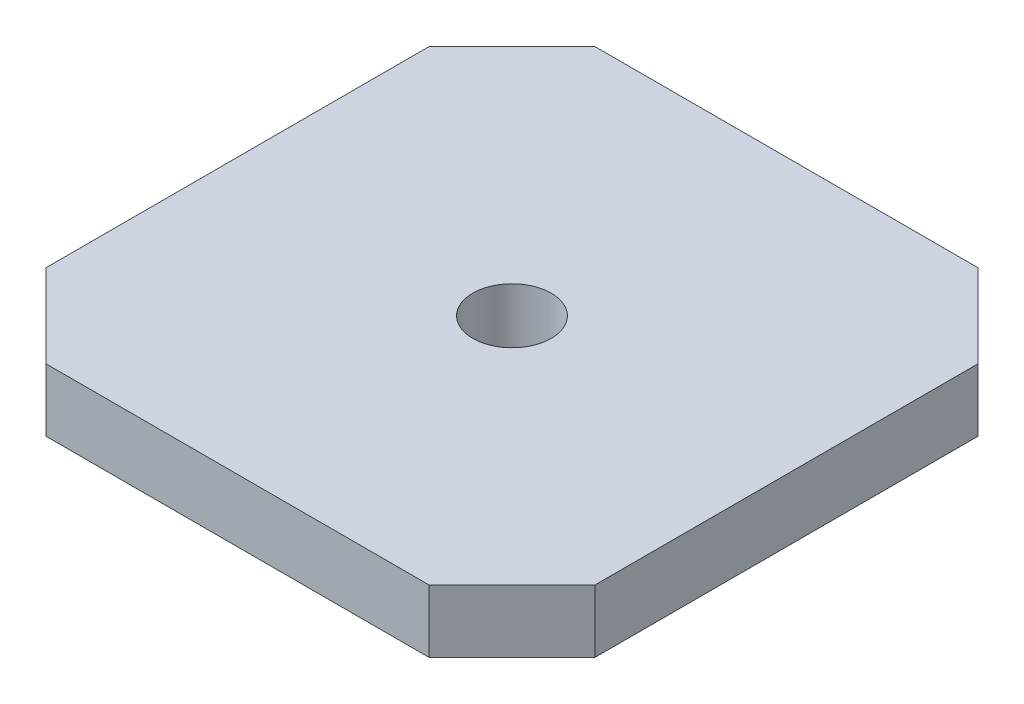
SolidWorks part; units mm, degrees
material "Hierro dúctil"
ref_plane "Alzado" through (0, 0, 0) normal (0, 0, 1) x (1, 0, 0)
ref_plane "Planta" through (0, 0, 0) normal (0, 1, 0) x (1, 0, 0)
ref_plane "Vista lateral" through (0, 0, 0) normal (1, 0, 0) x (0, 0, -1)
sketch "Croquis1" plane through (0, 0, 0) normal (0, 1, 0) x (1, 0, 0)
  line L1 (0, 0) -> (35, 0)
  line L2 (0, 0) -> (0, 35)
  line L3 (0, 35) -> (35, 35)
  line L4 (35, 0) -> (35, 35)
  dimension "D1" = 35
  dimension "D2" = 35
extrude "Saliente-Extruir1" add sketch "Croquis1" along normal blind 4
sketch "Croquis2" plane through (0, 4, 0) normal (0, 1, 0) x (1, 0, 0)
  line L0 (5.3015, 35) -> (0, 29.6985)
  line L1 (35, 35) -> (0, 35) construction
  line L2 (0, 35) -> (0, 0) construction
  line L3 (0, 29.6985) -> (0, 5.3015)
  line L4 (0, 5.3015) -> (5.3015, 0)
  line L5 (0, 0) -> (35, 0) construction
  line L6 (5.3015, 0) -> (29.6985, 0)
  line L7 (29.6985, 0) -> (35, 5.3015)
  line L8 (35, 0) -> (35, 35) construction
  line L9 (35, 5.3015) -> (35, 29.6985)
  line L10 (35, 29.6985) -> (29.6985, 35)
  line L11 (29.6985, 35) -> (5.3015, 35)
  dimension "D1" = 42
  dimension "D2" = 42
  dimension "D3" = 45
extrude "Cortar-Extruir2" cut sketch "Croquis2" against normal blind 18 flip side to cut
sketch "Croquis3" plane through (0, 4, 0) normal (0, 1, 0) x (1, 0, 0)
  line L0 (17.5, 35) -> (17.5, 0) construction
  line L1 (29.6985, 35) -> (5.3015, 35) construction
  line L2 (5.3015, 0) -> (29.6985, 0) construction
  circle A0 centre (17.5, 17.5) radius 2.5
  dimension "D1" = 5
extrude "Cortar-Extruir3" cut sketch "Croquis3" against normal through all
